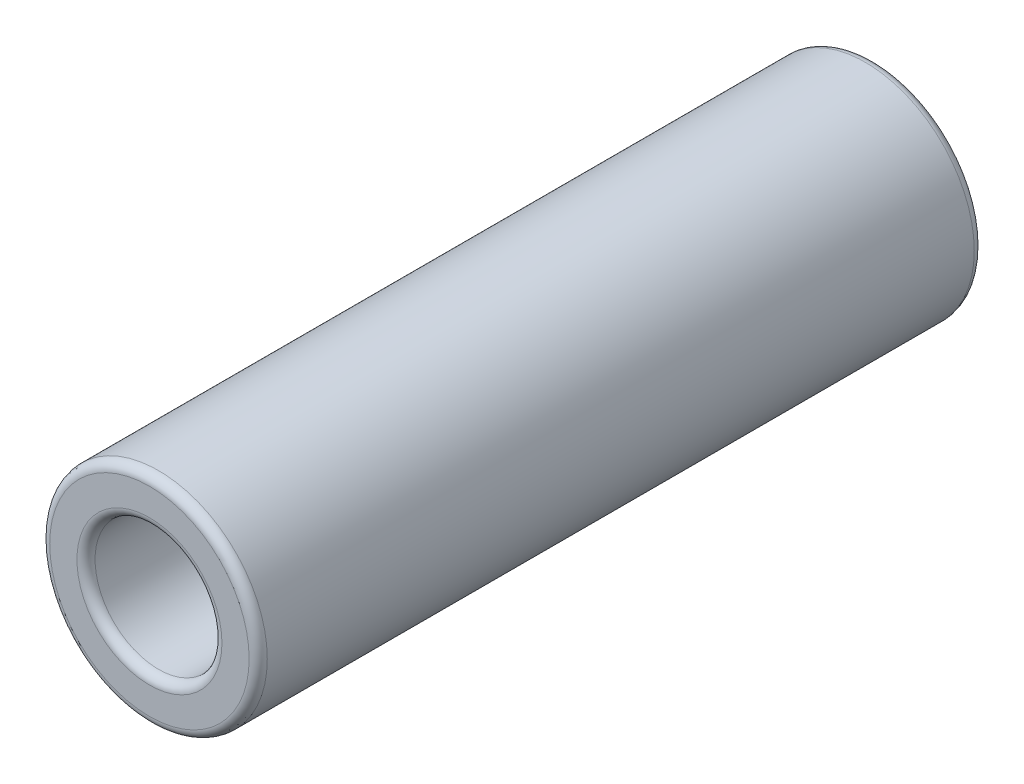
SolidWorks part; units mm, degrees
ref_plane "Płaszczyzna przednia" through (0, 0, 0) normal (0, 0, 1) x (1, 0, 0)
ref_plane "Płaszczyzna górna" through (0, 0, 0) normal (0, 1, 0) x (1, 0, 0)
ref_plane "Płaszczyzna prawa" through (0, 0, 0) normal (1, 0, 0) x (0, 0, -1)
sketch "Szkic1" plane through (0, 0, 0) normal (0, 0, 1) x (1, 0, 0)
  circle A0 centre (0, 0) radius 3.5
  circle A1 centre (0, 0) radius 6
  dimension "D1" = 7
  dimension "D2" = 12
extrude "Dodanie-wyciągnięcie1" add sketch "Szkic1" along normal blind 40
fillet "Zaokrąglenie2" radius 0.5 4 edges at (3.5, 0, 40) (6, 0, 40) (3.5, 0, 0) (6, 0, 0)
